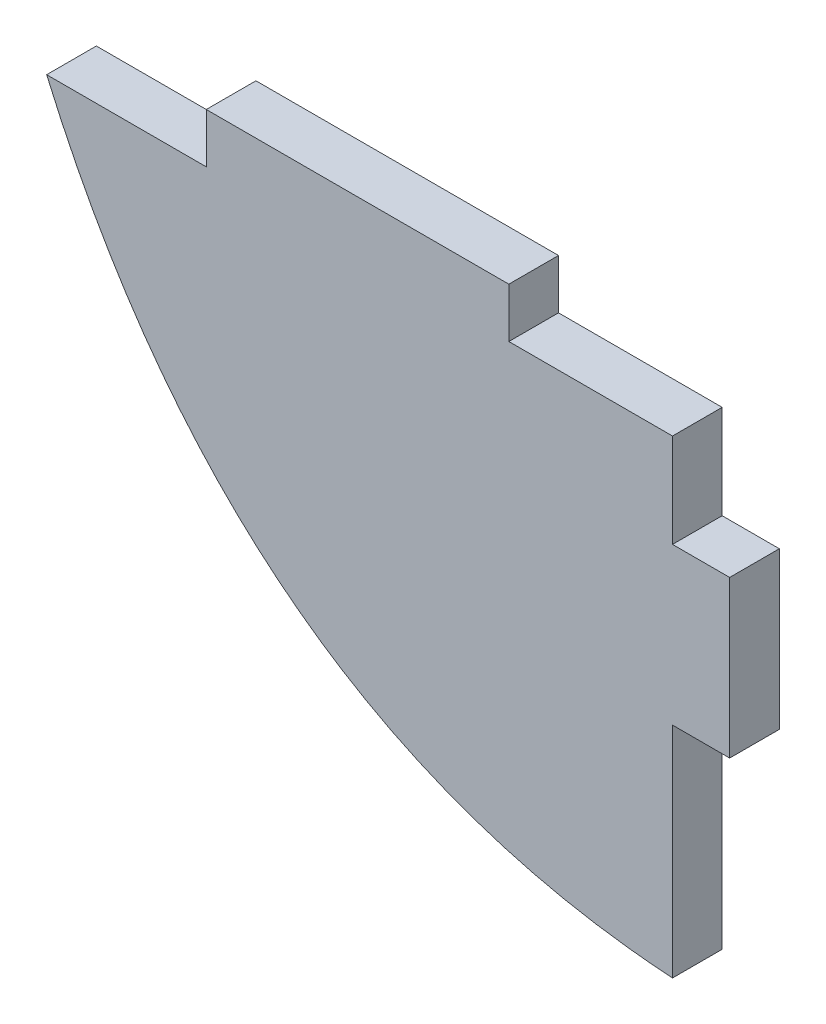
SolidWorks part; units mm, degrees
ref_plane "정면" through (0, 0, 0) normal (0, 0, 1) x (1, 0, 0)
ref_plane "윗면" through (0, 0, 0) normal (0, 1, 0) x (1, 0, 0)
ref_plane "우측면" through (0, 0, 0) normal (1, 0, 0) x (0, 0, -1)
sketch "Sketch1" plane through (0, 0, 0) normal (0, 0, 1) x (1, 0, 0)
  line L24 (-50.565, 9.3258) -> (-61.0251, 9.3258)
  line L35 (-50.565, 9.3258) -> (-50.565, 3.3258)
  line L36 (-80.3636, 9.3258) -> (-80.3636, 12.5008)
  line L41 (-80.3636, 12.5008) -> (-61.0251, 12.5008)
  line L42 (-61.0251, 12.5008) -> (-61.0251, 9.3258)
  line L43 (-80.3636, 9.3258) -> (-90.565, 9.3258)
  line L44 (-50.565, 3.3258) -> (-46.9113, 3.3258)
  line L49 (-46.9113, 3.3258) -> (-46.9113, -6.6742)
  line L50 (-46.9113, -6.6742) -> (-50.565, -6.6742)
  line L51 (-50.565, -6.6742) -> (-50.565, -20.6742)
  spline S0 degree 2 poles (-50.565, -20.6742) (-78.3512, -18.8709) (-90.565, 9.3258) knots 0 0 0 1 1 1
extrude "Boss-Extrude1" add sketch "Sketch1" along normal blind 3.175
